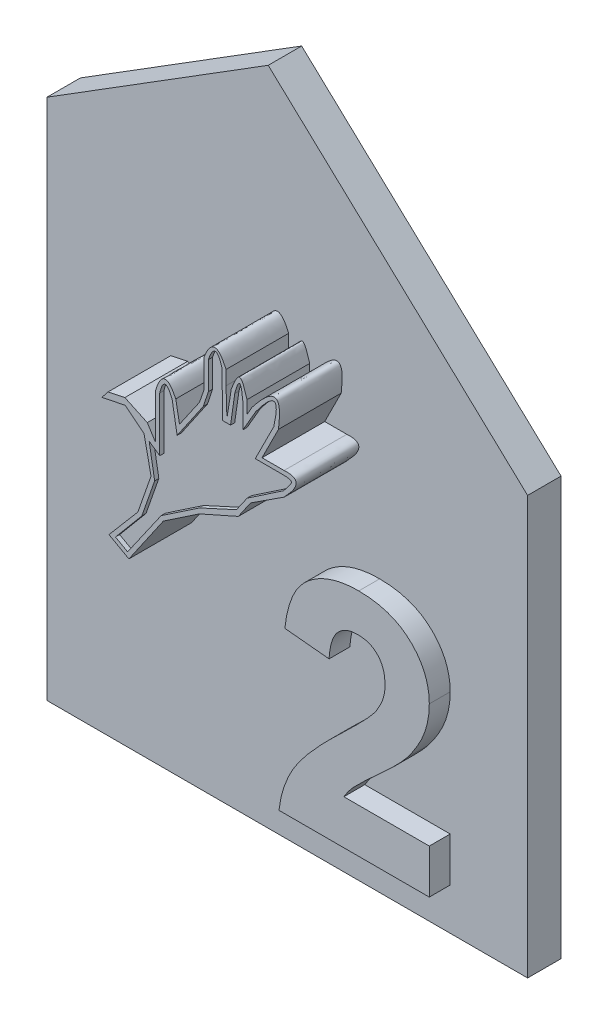
SolidWorks part; units mm, degrees
ref_plane "Přední rovina" through (0, 0, 0) normal (0, 0, 1) x (1, 0, 0)
ref_plane "Horní rovina" through (0, 0, 0) normal (0, 1, 0) x (1, 0, 0)
ref_plane "Pravá rovina" through (0, 0, 0) normal (1, 0, 0) x (0, 0, -1)
sketch "Skica1" plane through (0, 0, 0) normal (0, 0, 1) x (1, 0, 0)
  line L0 (-66.5051, 0) -> (66.5051, 0) construction
  line L1 (0, 0) -> (0, 20)
  line L2 (0, 20) -> (-12.4128, 31.6156)
  line L3 (-12.4128, 31.6156) -> (-23, 25)
  line L4 (-23, 25) -> (-23, 0)
  line L5 (-23, 0) -> (0, 0)
  dimension "D1" = 23
  dimension "D2" = 25
  dimension "D3" = 20
  dimension "D4" = 17
  dimension "D5" = 122
extrude "Přidat vysunutím5" add sketch "Skica1" along normal blind 1.6
sketch "Skica2" plane through (0, 0, 1.6) normal (0, 0, 1) x (1, 0, 0)
  line L1 (-23, 25) -> (-23, 0) construction
  line L2 (0, 0) -> (0, 20) construction
  line L3 (-3, 0) -> (-3, 22.8073) construction
  line L4 (-23, 0) -> (0, 0) construction
  line L5 (0, 20) -> (-12.4128, 31.6156) construction
  line L6 (-23, 2) -> (-3, 2) construction
  text T1 "2" font "Arial" height 11
  dimension "D2" = 3
  dimension "D3" = 2
extrude "Přidat vysunutím6" add sketch "Skica2" along normal blind 1
sketch "Skica3" plane through (0, 0, 1.6) normal (0, 0, 1) x (1, 0, 0)
  line L0 (-23, -0.3065) -> (-3.339, 23.1246) construction
  line L1 (-23, 25) -> (-23, 0) construction
  line L2 (0, 20) -> (-12.4128, 31.6156) construction
  line L3 (0, 0) -> (0, 20) construction
  line L4 (-23, 0) -> (0, 0) construction
  line L5 (-15.2007, 8.9884) -> (-6.4244, 19.4476)
  line L6 (-6.4244, 19.4476) -> (-11.7867, 23.9471)
  line L7 (-11.7867, 23.9471) -> (-20.563, 13.4879)
  line L8 (-20.563, 13.4879) -> (-15.2007, 8.9884)
  dimension "D1" = 3.339
  dimension "D2" = 50
  dimension "D3" = 7
  dimension "D4" = 13.6535
  dimension "D5" = 4.8
extrude "Přidat vysunutím7" add sketch "Skica3" along normal blind 3
sketch "Sketch3" plane through (0, 0, 4.6) normal (0, 0, 1) x (1, 0, 0)
  line L0 (-16.4575, 12.034) -> (-15.6492, 12.9843)
  line L1 (-16.0794, 10.8275) -> (-14.4276, 13.2233)
  line L3 (-14.4276, 13.2233) -> (-12.7028, 14.3815)
  line L7 (-10.8442, 15.2065) -> (-10.2572, 16.0579)
  line L11 (-8.6447, 17.1062) -> (-8.6519, 17.1062)
  line L13 (-8.6519, 18.2054) -> (-9.7081, 18.2054)
  line L14 (-9.7081, 18.2054) -> (-8.9203, 19.7766)
  line L23 (-12.4795, 21.0004) -> (-12.4795, 19.6434)
  line L24 (-12.4795, 19.6434) -> (-12.7028, 19.0038)
  line L25 (-12.7028, 19.0038) -> (-13.2857, 18.1584)
  line L26 (-13.2857, 18.1584) -> (-13.6577, 17.619)
  line L27 (-13.6577, 17.619) -> (-13.8345, 18.5811)
  line L30 (-14.8026, 18.4461) -> (-14.8026, 17.619)
  line L31 (-14.8026, 17.619) -> (-14.8026, 16.29)
  line L32 (-14.8026, 16.29) -> (-15.1995, 16.9166)
  line L46 (-16.4575, 12.034) -> (-17.0316, 11.3588)
  line L47 (-17.0316, 11.3588) -> (-16.0794, 10.8275)
  line L49 (-15.6492, 12.9843) -> (-15.0195, 14.7871)
  line L51 (-12.7028, 14.3815) -> (-10.8442, 15.2065)
  line L52 (-15.0195, 14.7871) -> (-15.3559, 16.3912)
  line L53 (-15.3559, 16.3912) -> (-15.866, 16.7949)
  line L54 (-15.866, 16.7949) -> (-16.2594, 17.1062)
  line L55 (-16.2594, 17.1062) -> (-17.3747, 16.8723)
  line L56 (-17.3747, 16.8723) -> (-17.0762, 17.2495)
  line L58 (-11.4308, 20.3252) -> (-11.4308, 21.0026)
  line L59 (-10.2572, 16.0579) -> (-8.6447, 17.1062)
  line L60 (-10.4258, 19.6434) -> (-10.1863, 20.055)
  line L62 (-10.4258, 19.6434) -> (-10.4258, 20.2554)
  line L64 (-11.1783, 20.3252) -> (-11.3887, 19.0038)
  line L65 (-11.3887, 19.0038) -> (-11.4308, 20.3252)
  line L66 (-17.0762, 17.2495) -> (-16.2707, 17.4184)
  line L67 (-16.2707, 17.4184) -> (-15.1995, 16.9166)
  line L76 (-11.7867, 23.9471) -> (-20.563, 13.4879)
  line L80 (-20.563, 13.4879) -> (-15.2007, 8.9884)
  line L81 (-15.2007, 8.9884) -> (-6.4244, 19.4476)
  line L82 (-6.4244, 19.4476) -> (-11.7867, 23.9471)
  spline S0 degree 2 poles (-11.4308, 21.0026) (-11.9834, 22.2851) (-12.4795, 21.0004) knots 0 0 0 1 1 1
  spline S1 degree 2 poles (-14.8026, 18.4461) (-14.4094, 19.767) (-13.8345, 18.5811) knots 0 0 0 1 1 1
  spline S2 degree 2 poles (-8.9203, 19.7766) (-8.6137, 22.0968) (-10.1863, 20.055) knots 0 0 0 1 1 1
  spline S3 degree 2 poles (-8.6519, 18.2054) (-7.4999, 18.2765) (-8.6519, 17.1062) knots 0 0 0 1 1 1
  spline S4 degree 3 poles (-11.1783, 20.3252) (-11.0421, 20.6632) (-10.762, 21.3583) (-10.5399, 20.6297) (-10.4258, 20.2554) knots 0 0 0 0 0.486294 1 1 1 1
  dimension "D1" = 1.743
  dimension "D2" = 2.2203
  dimension "D3" = 2.2275
  dimension "D4" = 2.4959
  dimension "D5" = 2.5988
  dimension "D6" = 3.2837
  dimension "D7" = 3.762
  dimension "D8" = 3.8328
  dimension "D9" = 4.0014
  dimension "D10" = 4.359
  dimension "D11" = 4.4198
  dimension "D12" = 4.7539
  dimension "D13" = 4.9643
  dimension "D14" = 5.0064
  dimension "D15" = 5.5534
  dimension "D16" = 6.0551
  dimension "D17" = 6.2785
  dimension "D18" = 6.8613
  dimension "D19" = 7.2333
  dimension "D20" = 7.4101
  dimension "D21" = 7.9146
  dimension "D22" = 8.0032
  dimension "D23" = 8.3782
  dimension "D24" = 8.5951
  dimension "D25" = 8.7751
  dimension "D26" = 8.9315
  dimension "D27" = 9.2248
  dimension "D28" = 9.4416
  dimension "D29" = 9.655
  dimension "D30" = 9.835
  dimension "D31" = 9.8463
  dimension "D32" = 10.0331
  dimension "D33" = 10.6072
  dimension "D34" = 10.6518
  dimension "D35" = 10.9503
  dimension "D36" = 0.1958
  dimension "D37" = 0.329
  dimension "D38" = 0.6075
  dimension "D39" = 0.8079
  dimension "D40" = 0.8777
  dimension "D41" = 1.5328
  dimension "D42" = 1.5529
  dimension "D43" = 1.555
  dimension "D44" = 2.1955
  dimension "D45" = 0.3054
  dimension "D46" = 0.4437
  dimension "D47" = 0.8664
  dimension "D48" = 1.0014
  dimension "D49" = 1.2422
  dimension "D50" = 1.2891
  dimension "D51" = 1.3117
  dimension "D52" = 2.0291
  dimension "D53" = 2.1981
  dimension "D54" = 2.3414
  dimension "D55" = 3.3897
  dimension "D56" = 2.5309
  dimension "D57" = 6.2243
  dimension "D58" = 7.4136
  dimension "D60" = 3.1575
  dimension "D64" = 5.0661
extrude "Cut-Extrude6" cut sketch "Sketch3" against normal blind 3
sketch "Sketch5" plane through (0, 0, 4.6) normal (0, 0, 1) x (1, 0, 0)
  line L0 (-12.2795, 20.9823) -> (-12.2795, 19.6562)
  line L1 (-12.2795, 19.6562) -> (-12.5173, 18.9291)
  line L2 (-12.4795, 21.0004) -> (-12.4795, 19.6434) construction
  line L3 (-14.846, 14.6774) -> (-15.4604, 12.9184)
  line L4 (-15.4604, 12.9184) -> (-16.7215, 11.4148)
  line L5 (-12.5173, 18.9291) -> (-13.7704, 17.1007)
  line L6 (-13.7704, 17.1007) -> (-14.0122, 18.4893)
  line L7 (-9.7081, 18.2054) -> (-8.9203, 19.7766) construction
  line L8 (-14.6028, 18.4362) -> (-14.6028, 15.8425)
  line L9 (-14.6028, 15.8425) -> (-15.1093, 16.1896)
  line L10 (-15.1093, 16.1896) -> (-14.846, 14.6774)
  line L11 (-15.3559, 16.3912) -> (-15.0195, 14.7871) construction
  line L12 (-16.1408, 11.0908) -> (-14.5365, 13.391)
  line L13 (-14.5365, 13.391) -> (-12.6985, 14.6315)
  line L14 (-12.6985, 14.6315) -> (-10.9311, 15.4409)
  line L15 (-10.9311, 15.4409) -> (-10.4162, 16.1792)
  line L16 (-10.4162, 16.1792) -> (-8.6749, 17.3543)
  line L17 (-15.0195, 14.7871) -> (-15.6492, 12.9843) construction
  line L18 (-15.6492, 12.9843) -> (-17.0316, 11.3588) construction
  line L19 (-17.0316, 11.3588) -> (-16.0794, 10.8275) construction
  line L20 (-9.1475, 19.7698) -> (-10.0322, 18.0054)
  line L21 (-16.0794, 10.8275) -> (-14.4276, 13.2233) construction
  line L22 (-16.1408, 11.0908) -> (-16.7215, 11.4148)
  line L23 (-8.8246, 18.0054) -> (-10.0322, 18.0054)
  line L24 (-11.0129, 20.2127) -> (-11.2154, 18.8038)
  line L25 (-10.0055, 19.9695) -> (-10.6258, 18.8997)
  line L26 (-10.6258, 18.8997) -> (-10.6258, 20.0778)
  line L27 (-11.2154, 18.8038) -> (-11.5884, 18.8038)
  line L28 (-11.5884, 18.8038) -> (-11.6288, 20.974)
  spline S0 degree 2 poles (-14.0122, 18.4893) (-14.3851, 19.3952) (-14.6028, 18.4362) knots 0 0 0 1 1 1
  spline S1 degree 3 poles (-8.6749, 17.3543) (-8.2559, 17.9129) (-8.0599, 18.0054) (-8.8246, 18.0054) knots 0 0 0 0 1 1 1 1
  spline S2 degree 2 poles (-9.1475, 19.7698) (-8.6831, 21.7777) (-10.0055, 19.9695) knots 0 0 0 1 1 1
  spline S3 degree 2 poles (-10.6258, 20.0778) (-10.7345, 21.342) (-11.0129, 20.2127) knots 0 0 0 1 1 1
  spline S4 degree 2 poles (-11.6288, 20.974) (-11.9253, 22.0189) (-12.2795, 20.9823) knots 0 0 0 1 1 1
  dimension "D29" = 0.2
  dimension "D34" = 0.2
  dimension "D41" = 2.3562
  dimension "D42" = 1.2221
  dimension "D1" = 0.2
  dimension "D2" = 0.2
  dimension "D3" = 0.2004
  dimension "D4" = 0.765
  dimension "D5" = 0.2
  dimension "D6" = 0.2
  dimension "D7" = 0.2
  dimension "D8" = 1.4096
  dimension "D9" = 0.2
  dimension "D10" = 0.1998
  dimension "D11" = 0.2
  dimension "D12" = 0.4398
  dimension "D13" = 0.3329
  dimension "D14" = 0.1521
  dimension "D15" = 0.2
  dimension "D16" = 0.2
  dimension "D17" = 0.2
  dimension "D18" = 0.2
  dimension "D19" = 0.2
  dimension "D20" = 1.8632
  dimension "D21" = 0.2
  dimension "D22" = 0.2
  dimension "D23" = 0.25
  dimension "D24" = 0.25
  dimension "D25" = 0.2
  dimension "D26" = 2.8044
  dimension "D27" = 2.2174
  dimension "D28" = 1.9439
  dimension "D30" = 0.2
  dimension "D31" = 0.25
  dimension "D32" = 0.2
  dimension "D33" = 0.2
  dimension "D35" = 0.2
  dimension "D36" = 0.2
  dimension "D37" = 0.2
  dimension "D38" = 0.9316
  dimension "D39" = 1.1781
  dimension "D40" = 1.2366
  dimension "D43" = 0.5729
  dimension "D44" = 0.3609
  dimension "D45" = 0.2
  dimension "D46" = 0.2034
  dimension "D47" = 0.2
  dimension "D48" = 0.2
  dimension "D49" = 0.2
  dimension "D50" = 1.4089
  dimension "D51" = 2.1702
extrude "Cut-Extrude7" cut sketch "Sketch5" against normal blind 0.2 contours S4 L0 L1 L5 L6 S0 L8 L9 L10 L3 L4 L22 L12 L13 L14 L15 L16 S1 L23 L20 S2 L25 L26 S3 L24 L27 L28
